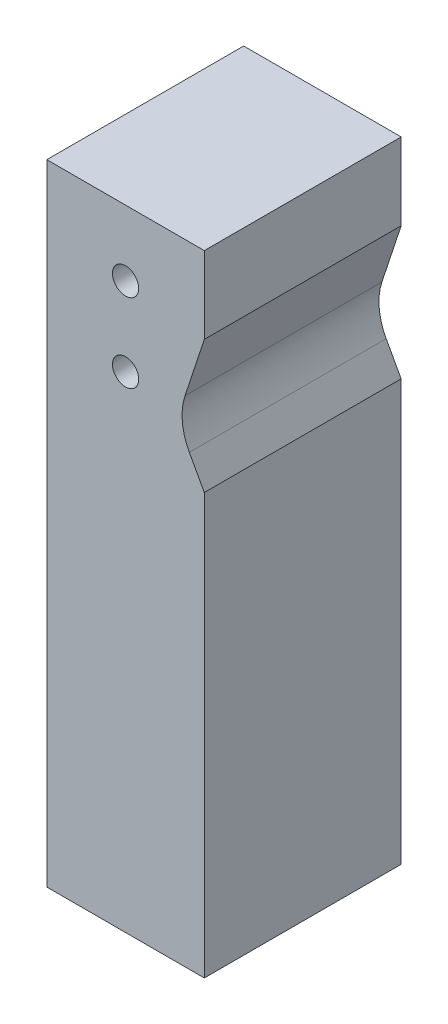
SolidWorks part; units mm, degrees
ref_plane "Front" through (0, 0, 0) normal (0, 0, 1) x (1, 0, 0)
ref_plane "Top" through (0, 0, 0) normal (0, 1, 0) x (1, 0, 0)
ref_plane "Right" through (0, 0, 0) normal (1, 0, 0) x (0, 0, -1)
sketch "Sketch1" plane through (0, 0, 0) normal (0, 0, 1) x (1, 0, 0)
  line L0 (0, -4.7625) -> (0, 4.7625) construction
  line L1 (-9.525, -63.5) -> (9.525, -63.5)
  line L2 (-9.525, -63.5) -> (-9.525, 12.7)
  line L3 (-9.525, 12.7) -> (9.525, 12.7)
  line L4 (9.525, -63.5) -> (9.525, 12.7)
  line L5 (0, 4.7625) -> (0, 12.7) construction
  circle A0 centre (0, 4.7625) radius 1.5875
  circle A1 centre (0, -4.7625) radius 1.5875
  point P0 (0, 0)
  point P13 (0, 0)
  dimension "D3" = 3.175
  dimension "D1" = 76.2
  dimension "D2" = 19.05
  dimension "D4" = 7.9375
  dimension "D5" = 9.525
extrude "Boss-Extrude1" add sketch "Sketch1" along normal blind 23.8125
sketch "Sketch3" plane through (0, 0, 23.8125) normal (0, 0, 1) x (1, 0, 0)
  line L0 (7.9476, -3.9126) -> (11.3477, 6.3857) construction
  line L1 (13.845, -18.8682) -> (8.4097, -8.9567) construction
  line L2 (9.525, -10.9905) -> (8.4097, -8.9567) construction
  line L3 (7.9476, -3.9126) -> (9.525, 0.8652) construction
  line L6 (9.525, -63.5) -> (9.525, 12.7) construction
  line L7 (9.525, -12.6413) -> (9.525, 3.3969)
  line L8 (9.525, -12.6413) -> (7.7137, -9.3383)
  line L9 (7.1938, -3.6637) -> (9.525, 3.3969)
  line L10 (7.1938, -3.6637) -> (8.7713, 1.114) construction
  line L11 (8.829, -11.3722) -> (7.7137, -9.3383) construction
  arc A0 (7.9476, -3.9126) -> (8.4097, -8.9567) centre (13.9774, -5.9034) ccw construction
  arc A1 (7.9476, -3.9126) -> (8.4097, -8.9567) centre (13.9774, -5.9034) ccw construction
  arc A2 (7.1938, -3.6637) -> (7.7137, -9.3383) centre (13.9774, -5.9034) ccw
  dimension "D1" = 0.7937
extrude "Cut-Extrude1" cut sketch "Sketch3" against normal up to next
